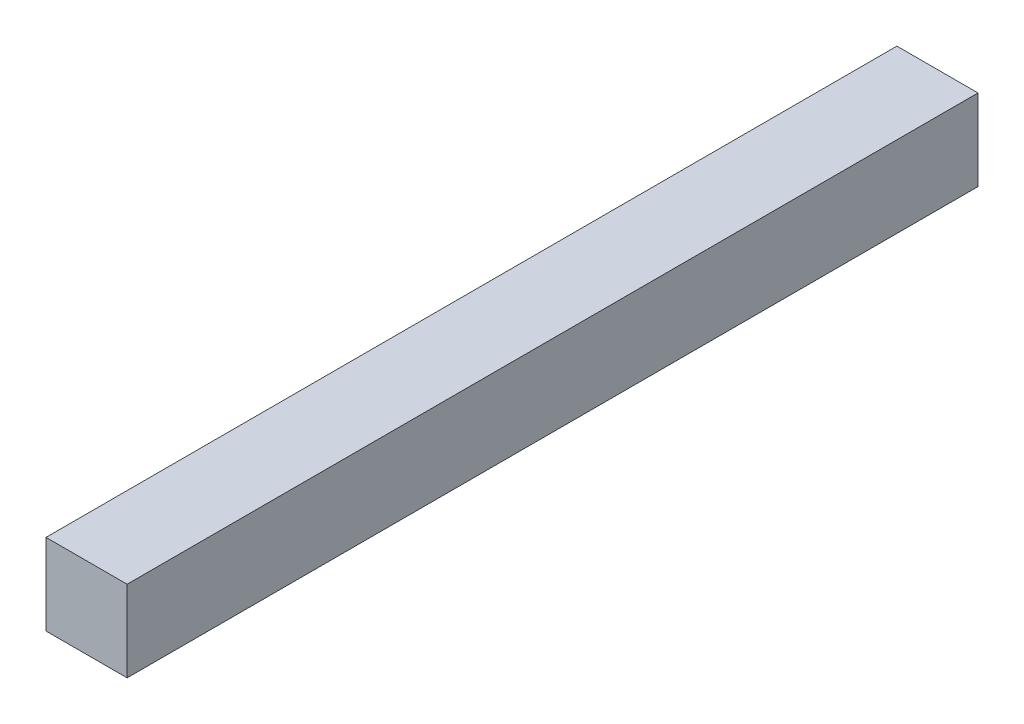
SolidWorks part; units mm, degrees
ref_plane "Front Plane" through (0, 0, 0) normal (0, 0, 1) x (1, 0, 0)
ref_plane "Top Plane" through (0, 0, 0) normal (0, 1, 0) x (1, 0, 0)
ref_plane "Right Plane" through (0, 0, 0) normal (1, 0, 0) x (0, 0, -1)
sketch "Sketch1" plane through (0, 0, 0) normal (0, 0, 1) x (1, 0, 0)
  line L1 (-133.2, 25.2) -> (-113.2, 25.2)
  line L2 (-133.2, 25.2) -> (-133.2, 5.2)
  line L3 (-133.2, 5.2) -> (-113.2, 5.2)
  line L4 (-113.2, 25.2) -> (-113.2, 5.2)
  dimension "D1" = 20
extrude "Boss-Extrude1" add sketch "Sketch1" along normal blind 209.8
